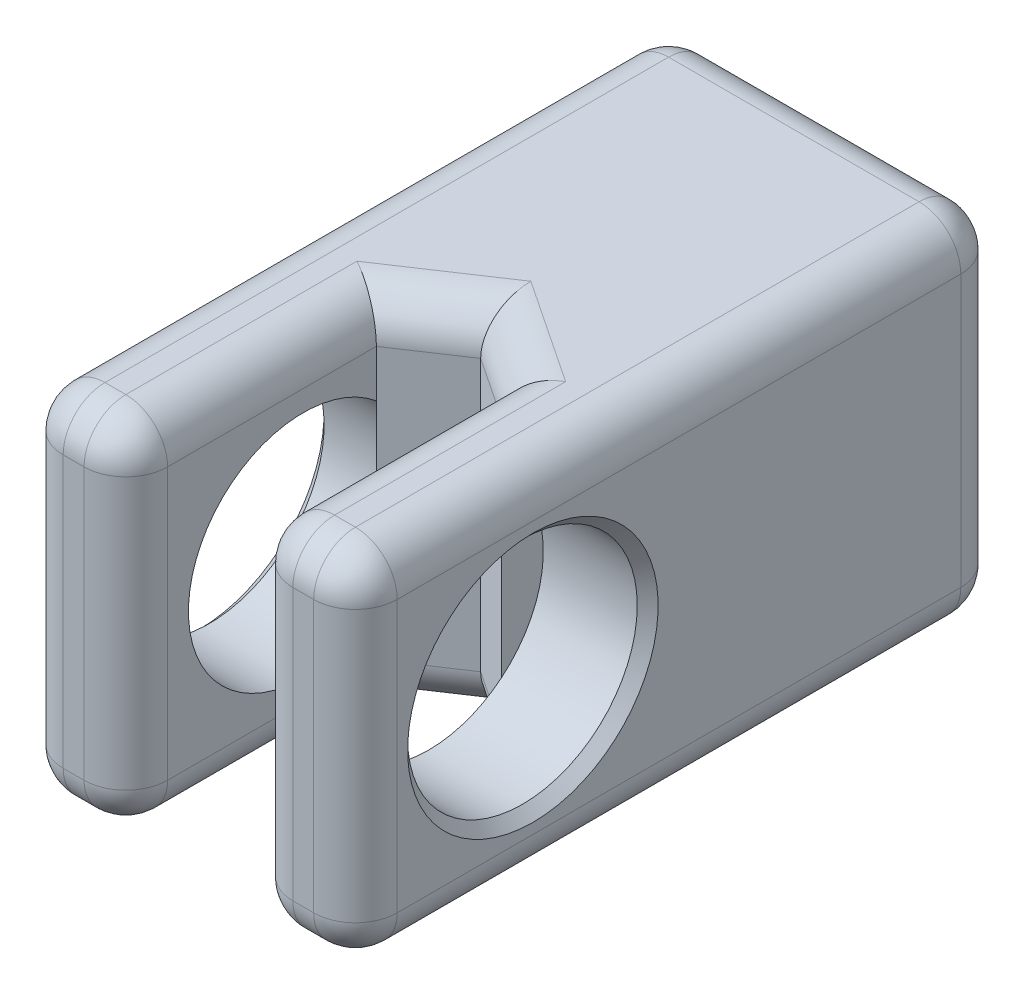
SolidWorks part; units mm, degrees
ref_plane "Front" through (0, 0, 0) normal (0, 0, 1) x (1, 0, 0)
ref_plane "Top" through (0, 0, 0) normal (0, 1, 0) x (1, 0, 0)
ref_plane "Right" through (0, 0, 0) normal (1, 0, 0) x (0, 0, -1)
sketch "Sketch1" plane through (0, 0, 0) normal (0, 0, 1) x (1, 0, 0)
  line L1 (-8, 8.5) -> (8, 8.5)
  line L2 (-8, 8.5) -> (-8, -8.5)
  line L3 (-8, -8.5) -> (8, -8.5)
  line L4 (8, 8.5) -> (8, -8.5)
  line L5 (-8, 8.5) -> (8, -8.5) construction
  line L6 (-8, -8.5) -> (8, 8.5) construction
  circle A0 centre (0, 0) radius 4
  dimension "D1" = 8
  dimension "D2" = 16
  dimension "D3" = 17
extrude "Boss-Extrude1" add sketch "Sketch1" along normal blind 15
sketch "Sketch2" plane through (0, 0, 15) normal (0, 0, 1) x (1, 0, 0)
  line L0 (-8, -8.5) -> (8, -8.5) construction
  line L2 (-8, 8.5) -> (-8, -8.5)
  line L3 (-8, -8.5) -> (-3, -8.5)
  line L4 (-3, 8.5) -> (-3, -8.5)
  line L5 (-3, 8.5) -> (-8, 8.5)
  line L7 (8, 8.5) -> (8, -8.5)
  line L8 (8, -8.5) -> (3, -8.5)
  line L9 (3, 8.5) -> (3, -8.5)
  line L10 (8, 8.5) -> (3, 8.5)
  dimension "D1" = 6
  dimension "D2" = 5
  dimension "D3" = 5
extrude "Boss-Extrude2" add sketch "Sketch2" along normal blind 16
sketch "Sketch3" plane through (-8, 0, 0) normal (-1, 0, 0) x (0, 0, 1)
  line L0 (22.5, 0) -> (0, 0) construction
  line L1 (0, 8.5) -> (0, -8.5) construction
  line L8 (15, -2.6458) -> (15, -8.5)
  line L9 (15, 2.6458) -> (15, -2.6458)
  line L10 (15, 8.5) -> (15, 2.6458)
  line L11 (31, 8.5) -> (15, 8.5)
  line L12 (31, -8.5) -> (31, 8.5)
  line L13 (15, -8.5) -> (31, -8.5)
  line L14 (15, -2.6458) -> (15, -8.5) construction
  line L15 (15, 2.6458) -> (15, -2.6458) construction
  circle A0 centre (22.5, 0) radius 5.5
  circle A1 centre (22.5, 0) radius 2.5 construction
  dimension "D1" = 11
  dimension "D4" = 5
  dimension "D3" = 7.5
  dimension "D2" = 0
extrude "Cut-Extrude3" cut sketch "Sketch3" against normal blind 16
sketch "Sketch4" plane through (0, -8.5, 0) normal (0, -1, 0) x (1, 0, 0)
  line L2 (3, 31) -> (3, 15) construction
  line L4 (-3, 31) -> (-3, 15) construction
  line L5 (-3, 19) -> (3, 19) construction
  line L6 (-3, 19) -> (-3, 15)
  line L7 (-3, 15) -> (0, 15)
  line L8 (3, 15) -> (3, 19)
  line L9 (0, 15) -> (3, 15)
  line L10 (0, 15) -> (0, 17) construction
  line L11 (-3, 19) -> (0, 17)
  line L12 (0, 17) -> (3, 19)
  dimension "D1" = 4
  dimension "D2" = 2
extrude "Boss-Extrude5" add sketch "Sketch4" against normal through all
sketch "Sketch5" plane through (0, 0, 15) normal (0, 0, -1) x (-1, 0, 0)
  circle A0 centre (0, 0) radius 1.25
  dimension "D1" = 2.5
extrude "Cut-Extrude4" cut sketch "Sketch5" against normal through all
fillet "Fillet1" radius 2 24 edges at (8, 8.5, 15.5) (3, 8.5, 25) (1.5, -8.5, 18) (1.5, 8.5, 18) (-1.5, 8.5, 18) (-1.5, -8.5, 18) (-3, 8.5, 25) (-8, 8.5, 15.5) (0, 8.5, 0) (8, 0, 31) (3, 0, 31) (-3, 0, 31) (-8, 0, 31) (-8, -8.5, 15.5) (-3, -8.5, 25) (3, -8.5, 25) (8, -8.5, 15.5) (0, -8.5, 0) (5.5, 8.5, 31) (-5.5, 8.5, 31) (-5.5, -8.5, 31) (5.5, -8.5, 31) (8, 0, 0) (-8, 0, 0)
chamfer "Chamfer1" distance 0.5 angle 45 3 edges at (8, -5.5, 22.5) (4, 0, 0) (-8, -5.5, 22.5)
equation "\"D3@Sketch1\"=17"
equation "\"D3@Sketch2\"=\"D2@Sketch2\""
